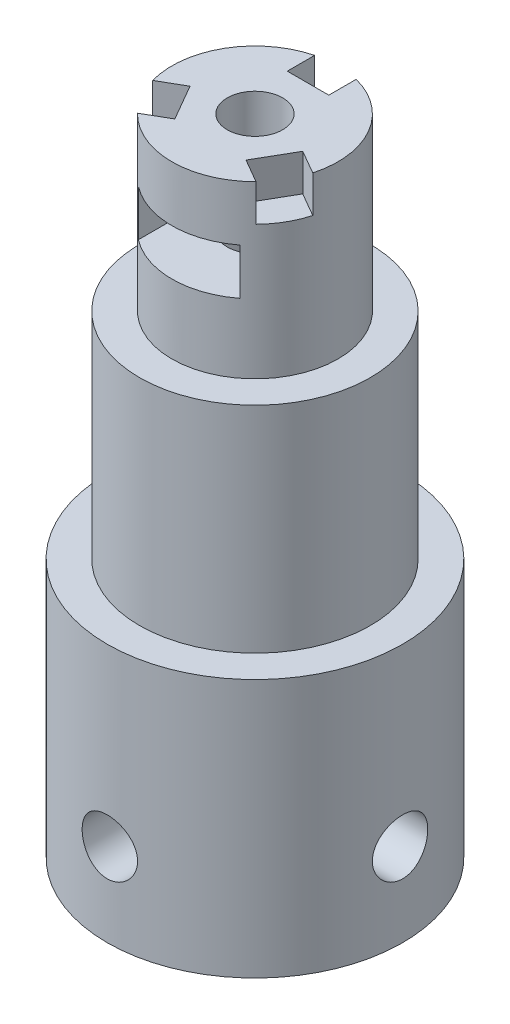
SolidWorks part; units mm, degrees
ref_plane "Front Plane" through (0, 0, 0) normal (0, 0, 1) x (1, 0, 0)
ref_plane "Top Plane" through (0, 0, 0) normal (0, 1, 0) x (1, 0, 0)
ref_plane "Right Plane" through (0, 0, 0) normal (1, 0, 0) x (0, 0, -1)
sketch "Sketch1" plane through (0, 0, 0) normal (0, 1, 0) x (1, 0, 0)
  circle A0 centre (0, 0) radius 3.125
  circle A1 centre (0, 0) radius 8
  dimension "D1" = 6.25
  dimension "D2" = 16
extrude "Boss-Extrude1" add sketch "Sketch1" along normal blind 14
sketch "Sketch2" plane through (0, 0, 0) normal (0, 0, 1) x (1, 0, 0)
  circle A0 centre (0, 4.5) radius 1.5
  dimension "D1" = 3
  dimension "D2" = 4.5
extrude "Cut-Extrude1" cut sketch "Sketch2" along normal through all both and the other way through all
sketch "Sketch3" plane through (0, 0, 0) normal (0, 0, 1) x (1, 0, 0)
  line L0 (-3.125, 0) -> (3.125, 0) construction
  line L1 (0, 1.3246) -> (2.75, 2.9123)
  line L2 (2.75, 2.9123) -> (2.75, 6.0877)
  line L3 (2.75, 6.0877) -> (0, 7.6754)
  line L4 (0, 7.6754) -> (-2.75, 6.0877)
  line L5 (-2.75, 6.0877) -> (-2.75, 2.9123)
  line L6 (-2.75, 2.9123) -> (0, 1.3246)
  line L7 (2.75, 2.9123) -> (-2.75, 2.9123)
  line L8 (2.75, 2.9123) -> (2.75, 0)
  line L9 (2.75, 0) -> (-2.75, 0)
  line L10 (-2.75, 2.9123) -> (-2.75, 0)
  circle A0 centre (0, 4.5) radius 2.75 construction
  dimension "D1" = 5.5
  dimension "D2" = 0
extrude "Cut-Extrude2" cut sketch "Sketch3" against normal blind 2.25 from offset 3.025 contours L6 L10 L9 L8 L1 | L7 L2 L3 L4 L5 | L1 L7 L6 offset against normal yes
sketch "Sketch4" plane through (0, 0, 0) normal (0, 0, 1) x (1, 0, 0)
  line L1 (0, 1.3246) -> (2.75, 2.9123)
  line L2 (2.75, 2.9123) -> (2.75, 6.0877)
  line L3 (2.75, 6.0877) -> (0, 7.6754)
  line L4 (0, 7.6754) -> (-2.75, 6.0877)
  line L5 (-2.75, 6.0877) -> (-2.75, 2.9123)
  line L6 (-2.75, 2.9123) -> (0, 1.3246)
  line L7 (2.75, 2.9123) -> (-2.75, 2.9123)
  line L8 (2.75, 2.9123) -> (2.75, 0)
  line L9 (2.75, 0) -> (-2.75, 0)
  line L10 (-2.75, 2.9123) -> (-2.75, 0)
  circle A0 centre (0, 4.5) radius 2.75 construction
  dimension "D1" = 5.5
extrude "Cut-Extrude3" cut sketch "Sketch4" along normal blind 2.25 from offset 3.025 contours L6 L10 L9 L8 L1 | L1 L7 L6 | L7 L2 L3 L4 L5
sketch "Sketch5" plane through (0, 14, 0) normal (0, 1, 0) x (1, 0, 0)
  circle A0 centre (0, 0) radius 6.25
  dimension "D1" = 12.5
extrude "Boss-Extrude2" add sketch "Sketch5" along normal blind 11.63
sketch "Sketch6" plane through (0, 25.63, 0) normal (0, 1, 0) x (1, 0, 0)
  circle A0 centre (0, 0) radius 4.5
  dimension "D1" = 9
extrude "Boss-Extrude3" add sketch "Sketch6" along normal blind 9.25
sketch "Sketch7" plane through (0, 34.88, 0) normal (0, 1, 0) x (1, 0, 0)
  circle A0 centre (0, 0) radius 1.5
  dimension "D1" = 3
extrude "Cut-Extrude4" cut sketch "Sketch7" against normal blind 8
sketch "Sketch8" plane through (0, 34.88, 0) normal (0, 1, 0) x (1, 0, 0)
  line L1 (0, -3.1754) -> (2.75, -1.5877)
  line L2 (2.75, -1.5877) -> (2.75, 1.5877)
  line L3 (2.75, 1.5877) -> (0, 3.1754)
  line L4 (0, 3.1754) -> (-2.75, 1.5877)
  line L5 (-2.75, 1.5877) -> (-2.75, -1.5877)
  line L6 (-2.75, -1.5877) -> (0, -3.1754)
  line L7 (-2.75, -1.5877) -> (2.75, -1.5877)
  line L8 (-2.75, -1.5877) -> (-2.75, -5.1467)
  line L9 (-2.75, -5.1467) -> (2.75, -5.1467)
  line L10 (2.75, -1.5877) -> (2.75, -5.1467)
  circle A0 centre (0, 0) radius 2.75 construction
  circle M1 centre (0, 0) radius 1.5
  circle M2 centre (0, 0) radius 4.5
  dimension "D1" = 5.5
extrude "Cut-Extrude5" cut sketch "Sketch8" against normal blind 2.5 from offset 3 contours L10 L1 L6 L8 M2 | L7 L6 L1 | L5 L7 L2 L3 L4 M1 offset against normal yes
sketch "Sketch9" plane through (0, 34.88, 0) normal (0, 1, 0) x (1, 0, 0)
  line L1 (-1.125, 6.125) -> (1.125, 6.125)
  line L2 (-1.125, 6.125) -> (-1.125, 2.875)
  line L3 (-1.125, 2.875) -> (1.125, 2.875)
  line L4 (1.125, 6.125) -> (1.125, 2.875)
  line L5 (-1.125, 6.125) -> (1.125, 2.875) construction
  line L6 (-1.125, 2.875) -> (1.125, 6.125) construction
  circle A0 centre (0, 0) radius 4.5 construction
  circle A1 centre (0, 0) radius 4.5 construction
  point P0 (0, 4.5)
  dimension "D1" = 2.25
  dimension "D2" = 3.25
extrude "Cut-Extrude6" cut sketch "Sketch9" against normal blind 2
pattern_circular "CirPattern1" count 3 over 360 about axis through (0, 0, 0) along (0, 1, 0) of "Cut-Extrude6"
pattern_circular "CirPattern3" count 2 every 90 about axis through (0, 0, 0) along (0, 1, 0) of "Cut-Extrude1"
equation "\"D2@Sketch1\"=\"D1@Sketch1\"+(3*2)+2*2-0.25"
